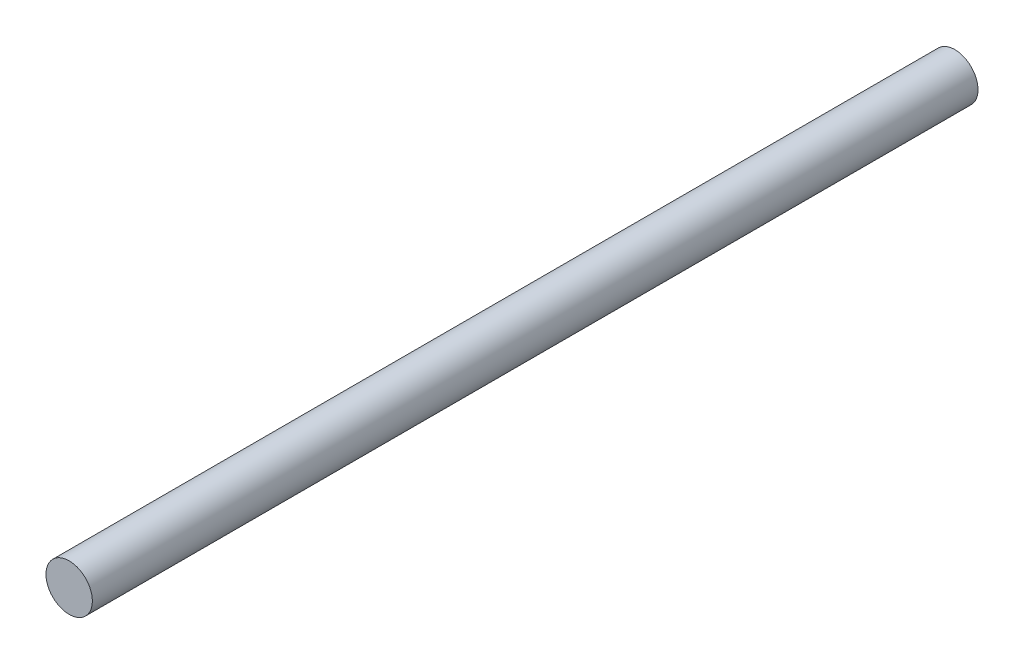
SolidWorks part; units mm, degrees
material "1060 Alloy"
ref_plane "Front Plane" through (0, 0, 0) normal (0, 0, 1) x (1, 0, 0)
ref_plane "Top Plane" through (0, 0, 0) normal (0, 1, 0) x (1, 0, 0)
ref_plane "Right Plane" through (0, 0, 0) normal (1, 0, 0) x (0, 0, -1)
sketch "Sketch1" plane through (0, 0, 0) normal (0, 0, 1) x (1, 0, 0)
  circle A0 centre (0, 0) radius 3
  dimension "D1" = 6
extrude "Boss-Extrude1" add sketch "Sketch1" along normal blind 114.5
